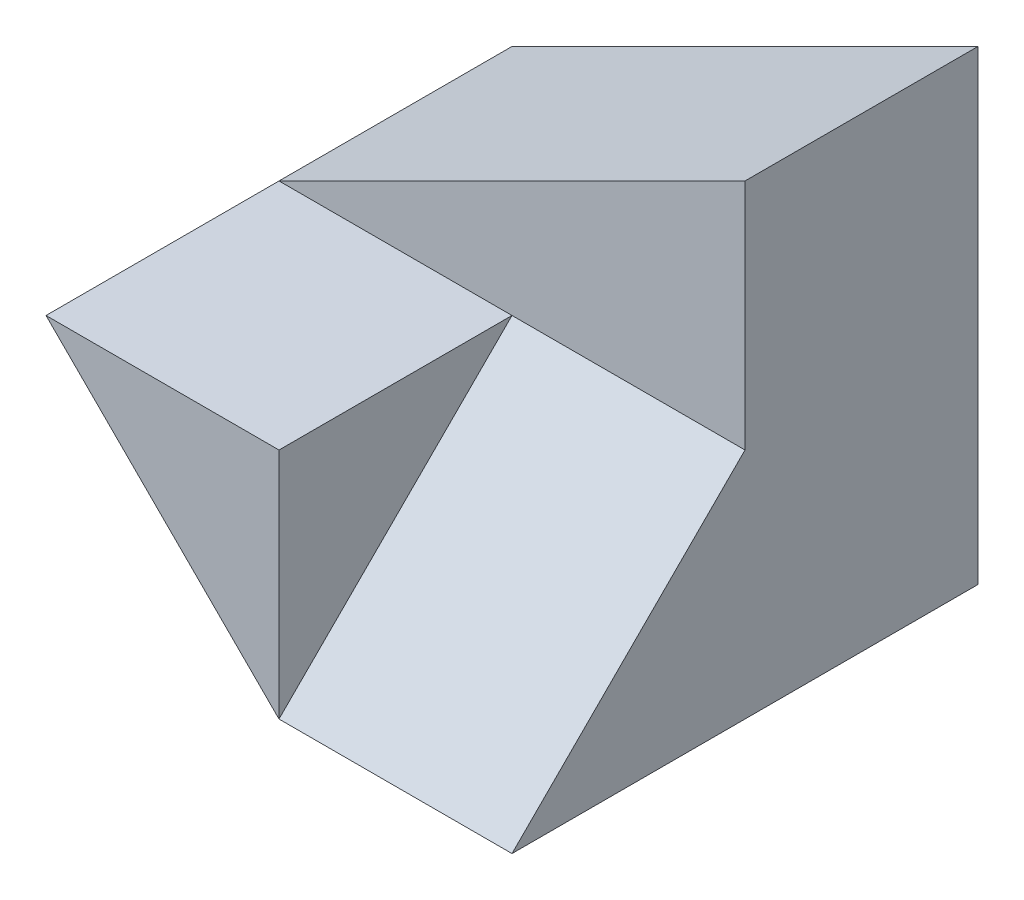
SolidWorks part; units mm, degrees
ref_plane "Front Plane" through (0, 0, 0) normal (0, 0, 1) x (1, 0, 0)
ref_plane "Top Plane" through (0, 0, 0) normal (0, 1, 0) x (1, 0, 0)
ref_plane "Right Plane" through (0, 0, 0) normal (1, 0, 0) x (0, 0, -1)
sketch "Sketch1" plane through (0, 0, 0) normal (0, 0, 1) x (1, 0, 0)
  line L1 (0, 0) -> (40, 0)
  line L2 (0, 0) -> (0, 40)
  line L3 (0, 40) -> (40, 40)
  line L4 (40, 0) -> (40, 40)
  dimension "D1" = 40
  dimension "D2" = 40
extrude "Boss-Extrude1" add sketch "Sketch1" along normal blind 40
sketch "Sketch2" plane through (0, 0, 40) normal (0, 0, 1) x (1, 0, 0)
  line L0 (40, 40) -> (0, 40)
  line L1 (0, 40) -> (0, 20)
  line L2 (0, 40) -> (0, 0) construction
  line L3 (0, 20) -> (40, 40)
extrude "Cut-Extrude1" cut sketch "Sketch2" against normal blind 40
sketch "Sketch3" plane through (40, 0, 0) normal (1, 0, 0) x (0, 0, -1)
  line L1 (-40, 40) -> (-20, 40)
  line L2 (-40, 40) -> (-40, 20)
  line L3 (-40, 20) -> (-20, 20)
  line L4 (-20, 40) -> (-20, 20)
  dimension "D1" = 20
  dimension "D2" = 20
extrude "Cut-Extrude2" cut sketch "Sketch3" against normal blind 40
sketch "Sketch4" plane through (0, 0, 40) normal (0, 0, 1) x (1, 0, 0)
  line L0 (0, 20) -> (20, 0)
  line L1 (0, 0) -> (40, 0) construction
  line L2 (20, 0) -> (0, 0)
  line L3 (0, 0) -> (0, 20)
extrude "Cut-Extrude4" cut sketch "Sketch4" against normal blind 40
sketch "Sketch5" plane through (40, 0, 0) normal (1, 0, 0) x (0, 0, -1)
  line L0 (-20, 20) -> (-40, 0)
  line L1 (-40, 0) -> (-40, 20)
  line L2 (-40, 20) -> (-20, 20)
extrude "Cut-Extrude5" cut sketch "Sketch5" against normal blind 20
